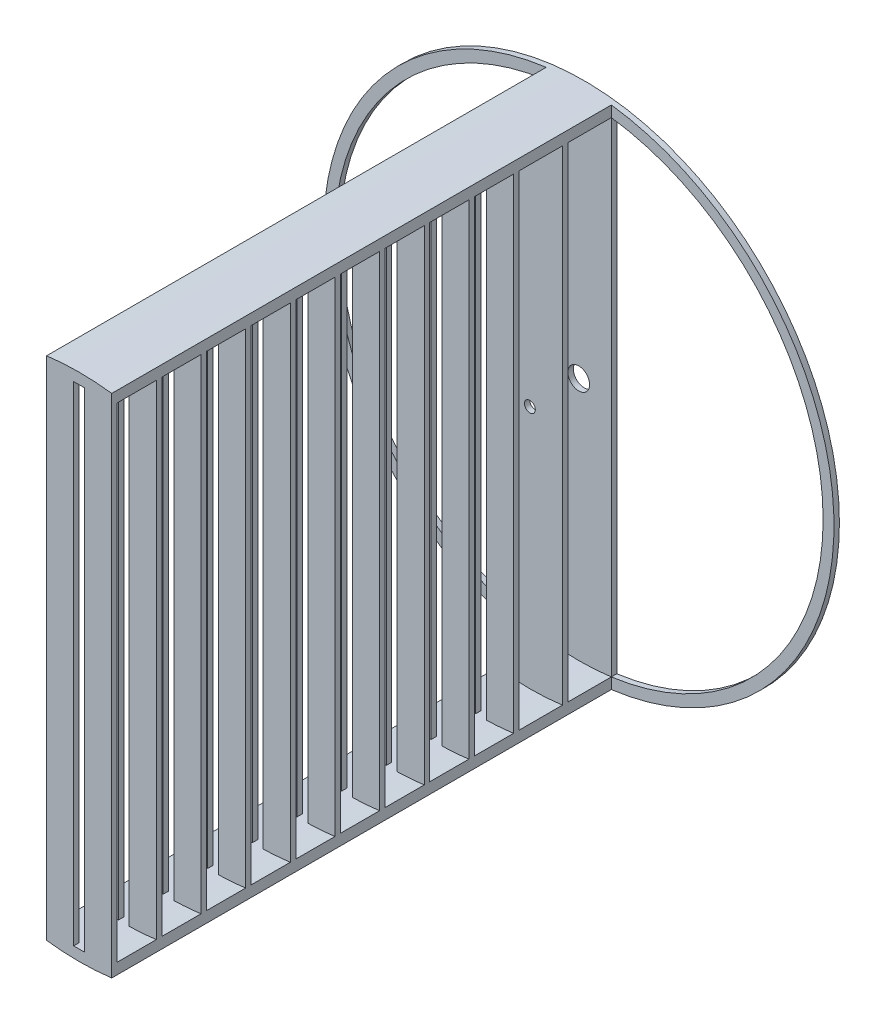
SolidWorks part; units mm, degrees
ref_plane "Front Plane" through (0, 0, 0) normal (0, 0, 1) x (1, 0, 0)
ref_plane "Top Plane" through (0, 0, 0) normal (0, 1, 0) x (1, 0, 0)
ref_plane "Right Plane" through (0, 0, 0) normal (1, 0, 0) x (0, 0, -1)
sketch "Sketch1" plane through (0, 0, 0) normal (0, 0, 1) x (1, 0, 0)
  line L0 (0, 0) -> (0, 596.9) construction
  line L1 (0, 0) -> (571.5, 0) construction
  line L2 (76.2, 566.3972) -> (76.2, -566.3972)
  line L3 (-76.2, 566.3972) -> (-76.2, -566.3972)
  circle A0 centre (0, 0) radius 609.6 construction
  circle A1 centre (0, 0) radius 609.6 construction
  circle A2 centre (0, 0) radius 596.9
  circle A4 centre (0, 0) radius 76.2 construction
  circle A5 centre (0, 0) radius 76.2 construction
  arc A8 (-76.2, -566.3972) -> (-76.2, 566.3972) centre (0, 0) cw
  arc A9 (76.2, -566.3972) -> (76.2, 566.3972) centre (0, 0) ccw
  circle A10 centre (0, 0) radius 25.4 construction
  circle A11 centre (0, 0) radius 25.4
  circle A12 centre (0, 0) radius 571.5 construction
  dimension "D2" = 25.4
  dimension "D1" = 12.7
extrude "Boss-Extrude1" add sketch "Sketch1" along normal blind 12.7
sketch "Sketch2" plane through (0, 0, 12.7) normal (0, 0, 1) x (1, 0, 0)
  line L0 (-76.2, -566.3972) -> (-76.2, -592.0162)
  line L1 (76.2, -566.3972) -> (76.2, -592.0162)
  circle A0 centre (0, 0) radius 596.9 construction
  circle A2 centre (0, 0) radius 596.9 construction
  circle A3 centre (0, 0) radius 609.6 construction
  circle A5 centre (0, 0) radius 571.5 construction
  circle A6 centre (0, 0) radius 609.6 construction
  circle A7 centre (0, 0) radius 571.5 construction
  arc A8 (76.2, -566.3972) -> (-76.2, -566.3972) centre (0, 0) cw
  arc A9 (76.2, -592.0162) -> (-76.2, -592.0162) centre (0, 0) cw
extrude "Boss-Extrude2" add sketch "Sketch2" along normal offset from surface (1168.4 mm away) 12.7
mirror "Mirror1" about plane through (0, 0, 0) normal (0, 1, 0) of "Boss-Extrude2"
ref_plane "Plane4" through (0, 0, 114.3) normal (0, 0, 1) x (1, 0, 0)
sketch "Sketch3" plane through (0, 0, 114.3) normal (0, 0, 1) x (1, 0, 0)
  line L0 (76.2, -592.0162) -> (76.2, 592.0162)
  line L1 (-76.2, -592.0162) -> (-76.2, 592.0162)
  line L2 (-76.2, 0) -> (76.2, 0) construction
  arc A0 (-76.2, -592.0162) -> (76.2, -592.0162) centre (0, 0) ccw construction
  arc A1 (-76.2, -592.0162) -> (76.2, -592.0162) centre (0, 0) ccw
  arc A2 (-76.2, 592.0162) -> (76.2, 592.0162) centre (0, 0) cw
  circle A3 centre (0, 0) radius 12.7
  point P5 (0, 0)
  dimension "D1" = 25.4
extrude "Boss-Extrude3" add sketch "Sketch3" along normal blind 12.7
ref_plane "Plane5" through (0, 0, 228.6) normal (0, 0, 1) x (1, 0, 0)
sketch "Sketch4" plane through (0, 0, 228.6) normal (0, 0, 1) x (1, 0, 0)
  line L0 (12.7, -571.3589) -> (12.7, 571.3589)
  line L1 (0, 0) -> (0, -596.9) construction
  line L2 (76.2, -592.0162) -> (76.2, 592.0162)
  line L3 (-76.2, 592.0162) -> (-76.2, -592.0162)
  line L4 (76.2, -592.0162) -> (76.2, 592.0162)
  line L5 (-76.2, 592.0162) -> (-76.2, -592.0162)
  line L6 (-12.7, -571.3589) -> (-12.7, 571.3589)
  line L7 (12.7, 0) -> (-12.7, 0) construction
  line L9 (0, 571.5) -> (0, -571.5) construction
  arc A0 (-76.2, -566.3972) -> (76.2, -566.3972) centre (0, 0) ccw construction
  arc A1 (-12.7, -571.3589) -> (12.7, -571.3589) centre (0, 0) ccw
  arc A3 (-12.7, 571.3589) -> (12.7, 571.3589) centre (0, 0) cw
  arc A4 (76.2, 592.0162) -> (-76.2, 592.0162) centre (0, 0) ccw
  arc A5 (-76.2, -592.0162) -> (76.2, -592.0162) centre (0, 0) ccw
  arc A6 (76.2, 592.0162) -> (-76.2, 592.0162) centre (0, 0) ccw
  arc A7 (-76.2, -592.0162) -> (76.2, -592.0162) centre (0, 0) ccw
  point P16 (0, 0)
  dimension "D1" = 25.4
  dimension "D3" = 1143
  dimension "D2" = 0
extrude "Boss-Extrude4" add sketch "Sketch4" along normal blind 12.7
pattern_linear "LPattern1" count 10 spacing 104.4222 along (0, 0, 1) of "Boss-Extrude4"
